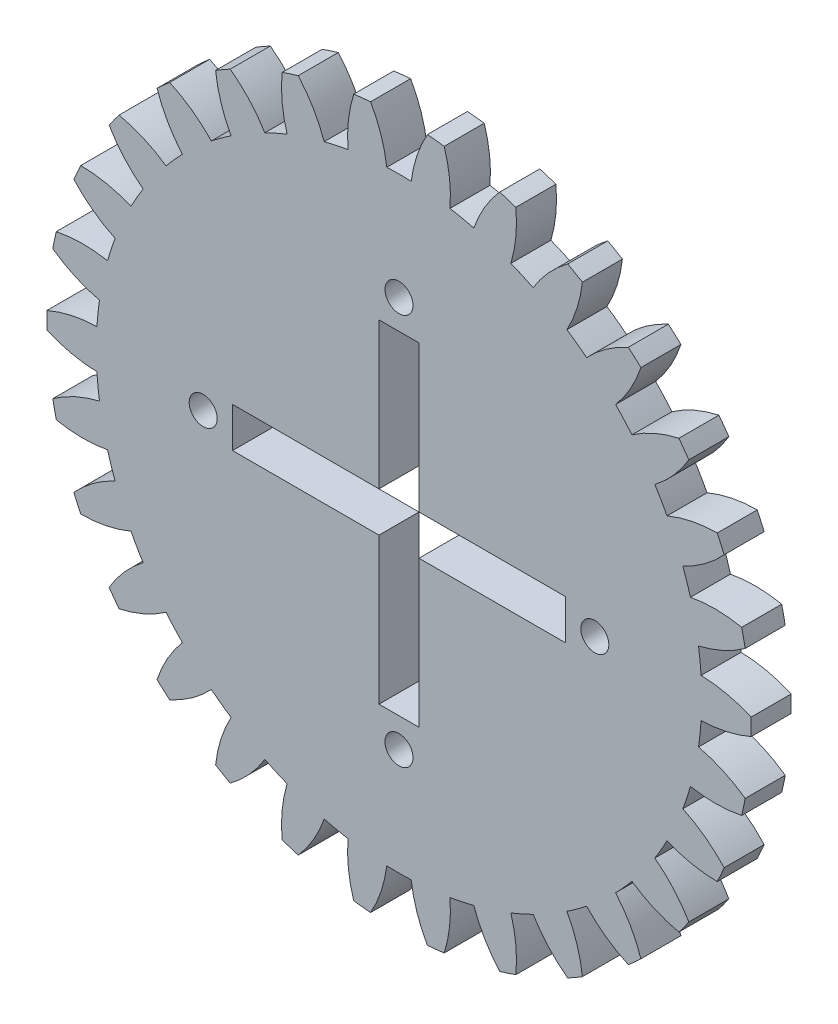
SolidWorks part; units mm, degrees
ref_plane "前视基准面" through (0, 0, 0) normal (0, 0, 1) x (1, 0, 0)
ref_plane "上视基准面" through (0, 0, 0) normal (0, 1, 0) x (1, 0, 0)
ref_plane "右视基准面" through (0, 0, 0) normal (1, 0, 0) x (0, 0, -1)
sketch "草图1" plane through (0, 0, 0) normal (0, 0, 1) x (1, 0, 0)
  arc A0 (-43.9873, -1.0569) -> (-37.7331, -2.4344) centre (-37.3786, 14.0618) ccw
  arc A1 (-37.7331, -2.4344) -> (-37.4146, -5.4639) centre (0, 0) ccw
  arc A2 (-37.4146, -5.4639) -> (-43.2458, -8.1117) centre (-33.6381, -21.5259) ccw
  arc A3 (-43.2458, -8.1117) -> (-42.8063, -10.1793) centre (0, 0) ccw
  arc A4 (-42.8063, -10.1793) -> (-36.4024, -10.2263) centre (-39.4854, 5.9831) ccw
  arc A5 (-36.4024, -10.2263) -> (-35.461, -13.1235) centre (0, 0) ccw
  arc A6 (-35.461, -13.1235) -> (-40.6143, -16.9257) centre (-28.4276, -28.0493) ccw
  arc A7 (-40.6143, -16.9257) -> (-39.7545, -18.8568) centre (0, 0) ccw
  arc A8 (-39.7545, -18.8568) -> (-33.4807, -17.5714) centre (-39.8665, -2.3572) ccw
  arc A9 (-33.4807, -17.5714) -> (-31.9576, -20.2095) centre (0, 0) ccw
  arc A10 (-31.9576, -20.2095) -> (-36.2077, -25) centre (-21.9746, -33.3468) ccw
  arc A11 (-36.2077, -25) -> (-34.9652, -26.7101) centre (0, 0) ccw
  arc A12 (-34.9652, -26.7101) -> (-29.0958, -24.1484) centre (-38.5052, -10.5943) ccw
  arc A13 (-29.0958, -24.1484) -> (-27.0575, -26.4122) centre (0, 0) ccw
  arc A14 (-27.0575, -26.4122) -> (-30.2187, -31.9817) centre (-14.5612, -37.1869) ccw
  arc A15 (-30.2187, -31.9817) -> (-28.6478, -33.3961) centre (0, 0) ccw
  arc A16 (-28.6478, -33.3961) -> (-23.4392, -29.6701) centre (-35.4611, -18.3685) ccw
  arc A17 (-23.4392, -29.6701) -> (-20.9748, -31.4606) centre (0, 0) ccw
  arc A18 (-20.9748, -31.4606) -> (-22.909, -37.5657) centre (-6.5114, -39.4017) ccw
  arc A19 (-22.909, -37.5657) -> (-21.0784, -38.6226) centre (0, 0) ccw
  arc A20 (-21.0784, -38.6226) -> (-16.7583, -33.895) centre (-30.8672, -25.3399) ccw
  arc A21 (-16.7583, -33.895) -> (-13.9754, -35.134) centre (0, 0) ccw
  arc A22 (-13.9754, -35.134) -> (-14.598, -41.5078) centre (1.8229, -39.8945) ccw
  arc A23 (-14.598, -41.5078) -> (-12.5877, -42.161) centre (0, 0) ccw
  arc A24 (-12.5877, -42.161) -> (-9.3449, -36.6385) centre (-24.9242, -31.2038) ccw
  arc A25 (-9.3449, -36.6385) -> (-6.3652, -37.2719) centre (0, 0) ccw
  arc A26 (-6.3652, -37.2719) -> (-5.649, -43.6359) centre (10.0776, -38.6437) ccw
  arc A27 (-5.649, -43.6359) -> (-3.5468, -43.8568) centre (0, 0) ccw
  arc A28 (-3.5468, -43.8568) -> (-1.5231, -37.7808) centre (-17.8919, -35.7039) ccw
  arc A29 (-1.5231, -37.7808) -> (1.5231, -37.7808) centre (0, 0) ccw
  arc A30 (1.5231, -37.7808) -> (3.5468, -43.8568) centre (17.8919, -35.7039) ccw
  arc A31 (3.5468, -43.8568) -> (5.649, -43.6359) centre (0, 0) ccw
  arc A32 (5.649, -43.6359) -> (6.3652, -37.2719) centre (-10.0776, -38.6437) ccw
  arc A33 (6.3652, -37.2719) -> (9.3449, -36.6385) centre (0, 0) ccw
  arc A34 (9.3449, -36.6385) -> (12.5877, -42.161) centre (24.9242, -31.2038) ccw
  arc A35 (12.5877, -42.161) -> (14.598, -41.5078) centre (0, 0) ccw
  arc A36 (14.598, -41.5078) -> (13.9754, -35.134) centre (-1.8229, -39.8945) ccw
  arc A37 (13.9754, -35.134) -> (16.7583, -33.895) centre (0, 0) ccw
  arc A38 (16.7583, -33.895) -> (21.0784, -38.6226) centre (30.8672, -25.3399) ccw
  arc A39 (21.0784, -38.6226) -> (22.909, -37.5657) centre (0, 0) ccw
  arc A40 (22.909, -37.5657) -> (20.9748, -31.4606) centre (6.5114, -39.4017) ccw
  arc A41 (20.9748, -31.4606) -> (23.4392, -29.6701) centre (0, 0) ccw
  arc A42 (23.4392, -29.6701) -> (28.6478, -33.3961) centre (35.4611, -18.3685) ccw
  arc A43 (28.6478, -33.3961) -> (30.2187, -31.9817) centre (0, 0) ccw
  arc A44 (30.2187, -31.9817) -> (27.0575, -26.4122) centre (14.5612, -37.1869) ccw
  arc A45 (27.0575, -26.4122) -> (29.0958, -24.1484) centre (0, 0) ccw
  arc A46 (29.0958, -24.1484) -> (34.9652, -26.7101) centre (38.5052, -10.5943) ccw
  arc A47 (34.9652, -26.7101) -> (36.2077, -25) centre (0, 0) ccw
  arc A48 (36.2077, -25) -> (31.9576, -20.2095) centre (21.9746, -33.3468) ccw
  arc A49 (31.9576, -20.2095) -> (33.4807, -17.5714) centre (0, 0) ccw
  arc A50 (33.4807, -17.5714) -> (39.7545, -18.8568) centre (39.8665, -2.3572) ccw
  arc A51 (39.7545, -18.8568) -> (40.6143, -16.9257) centre (0, 0) ccw
  arc A52 (40.6143, -16.9257) -> (35.461, -13.1235) centre (28.4276, -28.0493) ccw
  arc A53 (35.461, -13.1235) -> (36.4024, -10.2263) centre (0, 0) ccw
  arc A54 (36.4024, -10.2263) -> (42.8063, -10.1793) centre (39.4854, 5.9831) ccw
  arc A55 (42.8063, -10.1793) -> (43.2458, -8.1117) centre (0, 0) ccw
  arc A56 (43.2458, -8.1117) -> (37.4146, -5.4639) centre (33.6381, -21.5259) ccw
  arc A57 (37.4146, -5.4639) -> (37.7331, -2.4344) centre (0, 0) ccw
  arc A58 (37.7331, -2.4344) -> (43.9873, -1.0569) centre (37.3786, 14.0618) ccw
  arc A59 (43.9873, -1.0569) -> (43.9873, 1.0569) centre (0, 0) ccw
  arc A60 (43.9873, 1.0569) -> (37.7331, 2.4344) centre (37.3786, -14.0618) ccw
  arc A61 (37.7331, 2.4344) -> (37.4146, 5.4639) centre (0, 0) ccw
  arc A62 (37.4146, 5.4639) -> (43.2458, 8.1117) centre (33.6381, 21.5259) ccw
  arc A63 (43.2458, 8.1117) -> (42.8063, 10.1793) centre (0, 0) ccw
  arc A64 (42.8063, 10.1793) -> (36.4024, 10.2263) centre (39.4854, -5.9831) ccw
  arc A65 (36.4024, 10.2263) -> (35.461, 13.1235) centre (0, 0) ccw
  arc A66 (35.461, 13.1235) -> (40.6143, 16.9257) centre (28.4276, 28.0493) ccw
  arc A67 (40.6143, 16.9257) -> (39.7545, 18.8568) centre (0, 0) ccw
  arc A68 (39.7545, 18.8568) -> (33.4807, 17.5714) centre (39.8665, 2.3572) ccw
  arc A69 (33.4807, 17.5714) -> (31.9576, 20.2095) centre (0, 0) ccw
  arc A70 (31.9576, 20.2095) -> (36.2077, 25) centre (21.9746, 33.3468) ccw
  arc A71 (36.2077, 25) -> (34.9652, 26.7101) centre (0, 0) ccw
  arc A72 (34.9652, 26.7101) -> (29.0958, 24.1484) centre (38.5052, 10.5943) ccw
  arc A73 (29.0958, 24.1484) -> (27.0575, 26.4122) centre (0, 0) ccw
  arc A74 (27.0575, 26.4122) -> (30.2187, 31.9817) centre (14.5612, 37.1869) ccw
  arc A75 (30.2187, 31.9817) -> (28.6478, 33.3961) centre (0, 0) ccw
  arc A76 (28.6478, 33.3961) -> (23.4392, 29.6701) centre (35.4611, 18.3685) ccw
  arc A77 (23.4392, 29.6701) -> (20.9748, 31.4606) centre (0, 0) ccw
  arc A78 (20.9748, 31.4606) -> (22.909, 37.5657) centre (6.5114, 39.4017) ccw
  arc A79 (22.909, 37.5657) -> (21.0784, 38.6226) centre (0, 0) ccw
  arc A80 (21.0784, 38.6226) -> (16.7583, 33.895) centre (30.8672, 25.3399) ccw
  arc A81 (16.7583, 33.895) -> (13.9754, 35.134) centre (0, 0) ccw
  arc A82 (13.9754, 35.134) -> (14.598, 41.5078) centre (-1.8229, 39.8945) ccw
  arc A83 (14.598, 41.5078) -> (12.5877, 42.161) centre (0, 0) ccw
  arc A84 (12.5877, 42.161) -> (9.3449, 36.6385) centre (24.9242, 31.2038) ccw
  arc A85 (9.3449, 36.6385) -> (6.3652, 37.2719) centre (0, 0) ccw
  arc A86 (6.3652, 37.2719) -> (5.649, 43.6359) centre (-10.0776, 38.6437) ccw
  arc A87 (5.649, 43.6359) -> (3.5468, 43.8568) centre (0, 0) ccw
  arc A88 (3.5468, 43.8568) -> (1.5231, 37.7808) centre (17.8919, 35.7039) ccw
  arc A89 (1.5231, 37.7808) -> (-1.5231, 37.7808) centre (0, 0) ccw
  arc A90 (-1.5231, 37.7808) -> (-3.5468, 43.8568) centre (-17.8919, 35.7039) ccw
  arc A91 (-3.5468, 43.8568) -> (-5.649, 43.6359) centre (0, 0) ccw
  arc A92 (-5.649, 43.6359) -> (-6.3652, 37.2719) centre (10.0776, 38.6437) ccw
  arc A93 (-6.3652, 37.2719) -> (-9.3449, 36.6385) centre (0, 0) ccw
  arc A94 (-9.3449, 36.6385) -> (-12.5877, 42.161) centre (-24.9242, 31.2038) ccw
  arc A95 (-12.5877, 42.161) -> (-14.598, 41.5078) centre (0, 0) ccw
  arc A96 (-14.598, 41.5078) -> (-13.9754, 35.134) centre (1.8229, 39.8945) ccw
  arc A97 (-13.9754, 35.134) -> (-16.7583, 33.895) centre (0, 0) ccw
  arc A98 (-16.7583, 33.895) -> (-21.0784, 38.6226) centre (-30.8672, 25.3399) ccw
  arc A99 (-21.0784, 38.6226) -> (-22.909, 37.5657) centre (0, 0) ccw
  arc A100 (-22.909, 37.5657) -> (-20.9748, 31.4606) centre (-6.5114, 39.4017) ccw
  arc A101 (-20.9748, 31.4606) -> (-23.4392, 29.6701) centre (0, 0) ccw
  arc A102 (-23.4392, 29.6701) -> (-28.6478, 33.3961) centre (-35.4611, 18.3685) ccw
  arc A103 (-28.6478, 33.3961) -> (-30.2187, 31.9817) centre (0, 0) ccw
  arc A104 (-30.2187, 31.9817) -> (-27.0575, 26.4122) centre (-14.5612, 37.1869) ccw
  arc A105 (-27.0575, 26.4122) -> (-29.0958, 24.1484) centre (0, 0) ccw
  arc A106 (-29.0958, 24.1484) -> (-34.9652, 26.7101) centre (-38.5052, 10.5943) ccw
  arc A107 (-34.9652, 26.7101) -> (-36.2077, 25) centre (0, 0) ccw
  arc A108 (-36.2077, 25) -> (-31.9576, 20.2095) centre (-21.9746, 33.3468) ccw
  arc A109 (-31.9576, 20.2095) -> (-33.4807, 17.5714) centre (0, 0) ccw
  arc A110 (-33.4807, 17.5714) -> (-39.7545, 18.8568) centre (-39.8665, 2.3572) ccw
  arc A111 (-39.7545, 18.8568) -> (-40.6143, 16.9257) centre (0, 0) ccw
  arc A112 (-40.6143, 16.9257) -> (-35.461, 13.1235) centre (-28.4276, 28.0493) ccw
  arc A113 (-35.461, 13.1235) -> (-36.4024, 10.2263) centre (0, 0) ccw
  arc A114 (-36.4024, 10.2263) -> (-42.8063, 10.1793) centre (-39.4854, -5.9831) ccw
  arc A115 (-42.8063, 10.1793) -> (-43.2458, 8.1117) centre (0, 0) ccw
  arc A116 (-43.2458, 8.1117) -> (-37.4146, 5.4639) centre (-33.6381, 21.5259) ccw
  arc A117 (-37.4146, 5.4639) -> (-37.7331, 2.4344) centre (0, 0) ccw
  arc A118 (-37.7331, 2.4344) -> (-43.9873, 1.0569) centre (-37.3786, -14.0618) ccw
  arc A119 (-43.9873, 1.0569) -> (-43.9873, -1.0569) centre (0, 0) ccw
extrude "凸台-拉伸1" add sketch "草图1" along normal blind 5
sketch "草图3" plane through (0, 0, 5) normal (0, 0, 1) x (1, 0, 0)
  line L0 (2.5, 2.5) -> (2.5, 20.79)
  line L1 (20.79, -2.5) -> (2.5, -2.5)
  line L2 (20.79, -2.5) -> (20.79, 2.5)
  line L3 (20.79, 2.5) -> (2.5, 2.5)
  line L4 (-20.79, -2.5) -> (-20.79, 2.5)
  line L5 (0, 2.5) -> (0, 0) construction
  line L6 (20.79, 0) -> (-20.79, 0) construction
  line L7 (-2.5, -20.79) -> (2.5, -20.79)
  line L8 (-2.5, -20.79) -> (-2.5, -2.5)
  line L9 (-2.5, 20.79) -> (2.5, 20.79)
  line L10 (2.5, -20.79) -> (2.5, -2.5)
  line L11 (0, 20.79) -> (0, 0) construction
  line L12 (-2.5, 0) -> (2.5, 0) construction
  line L13 (-2.5, 2.5) -> (-20.79, 2.5)
  line L14 (-2.5, 2.5) -> (-2.5, 20.79)
  line L16 (-2.5, -2.5) -> (-20.79, -2.5)
  point P0 (0, 0)
  point P4 (0, 0)
  dimension "D1" = 5
  dimension "D2" = 5
  dimension "D3" = 18.29
  dimension "D4" = 18.29
  dimension "D5" = 18.29
extrude "切除-拉伸2" cut sketch "草图3" against normal blind 10
sketch "草图4" plane through (0, 0, 5) normal (0, 0, 1) x (1, 0, 0)
  circle A0 centre (0, 0) radius 24.46 construction
  circle A1 centre (0, 24.46) radius 1.75
  circle A2 centre (24.46, 0) radius 1.75
  circle A3 centre (0, -24.46) radius 1.75
  circle A4 centre (-24.46, 0) radius 1.75
  point P14 (0, 0)
  dimension "D1" = 48.92
  dimension "D2" = 3.5
  dimension "D3" = 4
extrude "切除-拉伸3" cut sketch "草图4" against normal blind 10
